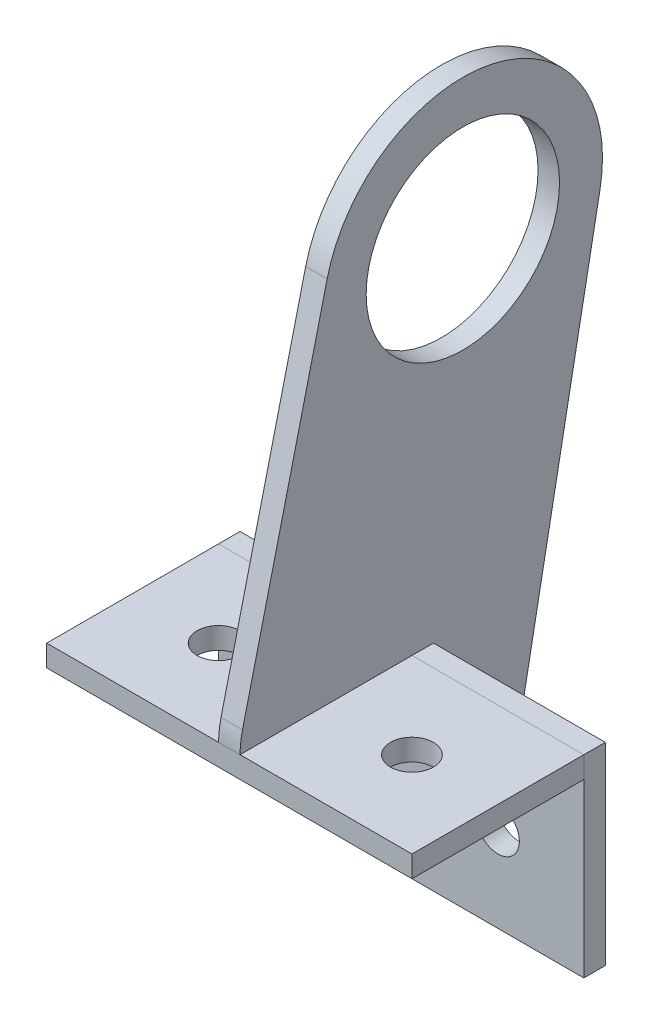
SolidWorks part; units mm, degrees
material "6061-T6 (SS)"
ref_plane "Front Plane" through (0, 0, 0) normal (0, 0, 1) x (1, 0, 0)
ref_plane "Top Plane" through (0, 0, 0) normal (0, 1, 0) x (1, 0, 0)
ref_plane "Right Plane" through (0, 0, 0) normal (1, 0, 0) x (0, 0, -1)
sketch "Sketch1" plane through (0, 0, 0) normal (1, 0, 0) x (0, 0, -1)
  line L0 (20.2754, -3.8489) -> (8.1272, -67.8436)
  line L1 (-4.35, -78.175) -> (-4.35, -49.6)
  line L2 (-7.525, -78.175) -> (-32.925, -78.175) construction
  line L5 (-7.525, -52.775) -> (-7.525, -78.175) construction
  line L7 (-32.925, -52.775) -> (-7.525, -52.775) construction
  line L8 (-4.35, -49.6) -> (-32.925, -49.6)
  line L9 (-32.5657, -46.6003) -> (-20.0536, 4.8745)
  circle A0 centre (0, 0) radius 14.2875
  circle A1 centre (0, 0) radius 20.6375 construction
  arc A2 (8.1272, -67.8436) -> (-4.35, -78.175) centre (-4.35, -65.475) cw
  arc A3 (20.2754, -3.8489) -> (-20.0536, 4.8745) centre (0, 0) ccw
  arc A4 (-32.925, -49.6) -> (-32.5657, -46.6003) centre (-20.225, -49.6) cw
  dimension "D1" = 28.575
  dimension "D2" = 41.275
  dimension "D3" = 12.7
  dimension "D7" = 12.7
  dimension "D4" = 3.175
  dimension "D5" = 3.175
  dimension "D6" = 28.575
extrude "Boss-Extrude1" add sketch "Sketch1" along normal mid plane 3.175
sketch "Sketch2" plane through (0, 0, 4.35) normal (0, 0, 1) x (1, 0, 0)
  line L0 (26.9875, -49.6) -> (-26.9875, -78.175) construction
  line L1 (-26.9875, -49.6) -> (26.9875, -49.6)
  line L2 (-26.9875, -49.6) -> (-26.9875, -78.175)
  line L3 (-26.9875, -78.175) -> (26.9875, -78.175)
  line L4 (26.9875, -49.6) -> (26.9875, -78.175)
  line L5 (-26.9875, -49.6) -> (26.9875, -78.175) construction
  line L7 (1.5875, -78.175) -> (-1.5875, -78.175) construction
  line L9 (-14.2875, -65.475) -> (14.2875, -65.475) construction
  circle A0 centre (-14.2875, -65.475) radius 3.175
  circle A1 centre (14.2875, -65.475) radius 3.175
  point P4 (0, -63.8875)
  point P12 (0, -65.475)
  dimension "D3" = 6.35
  dimension "D1" = 53.975
  dimension "D2" = 28.575
  dimension "D4" = 12.7
  dimension "D5" = 12.7
extrude "Boss-Extrude2" add sketch "Sketch2" along normal blind 3.175 separate body
sketch "Sketch3" plane through (0, 0, 7.525) normal (0, 0, 1) x (1, 0, 0)
  line L0 (-26.9875, -49.6) -> (-26.9875, -78.175) construction
  line L1 (-26.9875, -49.6) -> (26.9875, -49.6)
  line L2 (-26.9875, -49.6) -> (-26.9875, -52.775)
  line L3 (-26.9875, -52.775) -> (26.9875, -52.775)
  line L4 (26.9875, -49.6) -> (26.9875, -52.775)
  line L5 (-26.9875, -49.6) -> (26.9875, -52.775) construction
  line L6 (-26.9875, -52.775) -> (26.9875, -49.6) construction
  line L7 (26.9875, -78.175) -> (26.9875, -49.6) construction
  line L8 (-26.9875, -78.175) -> (26.9875, -78.175) construction
  point P4 (0, -51.1875)
  dimension "D1" = 3.175
  dimension "D2" = 25.4
extrude "Boss-Extrude3" add sketch "Sketch3" along normal blind 25.4 separate body
sketch "Sketch4" plane through (0, -49.6, 0) normal (0, 1, 0) x (1, 0, 0)
  line L0 (-14.2875, -20.225) -> (14.2875, -20.225) construction
  line L1 (-26.9875, -32.925) -> (-26.9875, -7.525) construction
  line L2 (26.9875, -7.525) -> (-26.9875, -7.525) construction
  circle A0 centre (-14.2875, -20.225) radius 3.175
  circle A1 centre (14.2875, -20.225) radius 3.175
  point P5 (0, -20.225)
  dimension "D1" = 6.35
  dimension "D2" = 12.7
  dimension "D3" = 12.7
extrude "Cut-Extrude1" cut sketch "Sketch4" against normal through all
